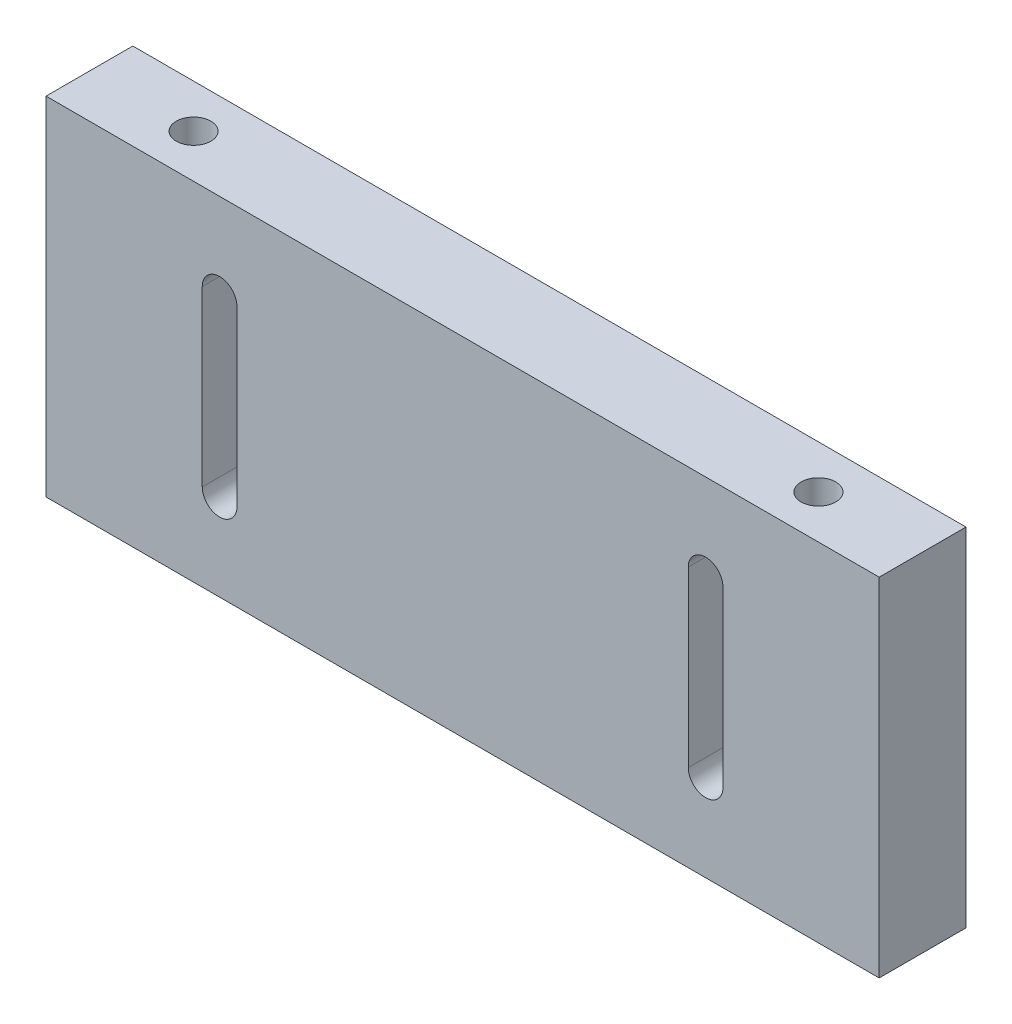
SolidWorks part; units mm, degrees
ref_plane "Alzado" through (0, 0, 0) normal (0, 0, 1) x (1, 0, 0)
ref_plane "Planta" through (0, 0, 0) normal (0, 1, 0) x (1, 0, 0)
ref_plane "Vista lateral" through (0, 0, 0) normal (1, 0, 0) x (0, 0, -1)
sketch "Croquis1" plane through (0, 0, 0) normal (0, 1, 0) x (1, 0, 0)
  line L1 (-120, 9.7222) -> (120, 9.7222)
  line L2 (-120, 9.7222) -> (-120, -15.2778)
  line L3 (-120, -15.2778) -> (120, -15.2778)
  line L4 (120, 9.7222) -> (120, -15.2778)
  dimension "D1" = 25
  dimension "D2" = 240
  dimension "D3" = 120
extrude "Saliente-Extruir1" add sketch "Croquis1" against normal blind 100
sketch "Croquis3" plane through (0, 0, 0) normal (0, 1, 0) x (1, 0, 0)
  line L0 (-120, 9.7222) -> (-120, -15.2778) construction
  line L1 (-120, -15.2778) -> (120, -15.2778) construction
  line L2 (120, -15.2778) -> (120, 9.7222) construction
  circle A0 centre (-90, -2.7778) radius 5
  circle A1 centre (90, -2.7778) radius 5
  dimension "D1" = 10
  dimension "D2" = 30
  dimension "D4" = 10
  dimension "D6" = 12.5
  dimension "D3" = 12.5
  dimension "D5" = 30
extrude "Cortar-Extruir1" cut sketch "Croquis3" against normal blind 25
sketch "Croquis4" plane through (0, 0, 15.2778) normal (0, 0, 1) x (1, 0, 0)
  line L0 (-120, -100) -> (120, -100) construction
  line L2 (-75, -25) -> (-75, -75)
  line L4 (-65, -25) -> (-65, -75)
  line L6 (65, -25) -> (65, -75)
  line L8 (75, -25) -> (75, -75)
  line L9 (-120, -100) -> (-120, 0) construction
  line L10 (120, -100) -> (120, 0) construction
  arc A0 (-65, -25) -> (-75, -25) centre (-70, -25) ccw
  arc A1 (-75, -75) -> (-65, -75) centre (-70, -75) ccw
  arc A2 (65, -75) -> (75, -75) centre (70, -75) ccw
  arc A3 (75, -25) -> (65, -25) centre (70, -25) ccw
  dimension "D9" = 10
  dimension "D1" = 50
  dimension "D2" = 50
  dimension "D3" = 10
  dimension "D4" = 10
  dimension "D6" = 25
  dimension "D7" = 50
  dimension "D8" = 50
extrude "Cortar-Extruir2" cut sketch "Croquis4" against normal blind 25
